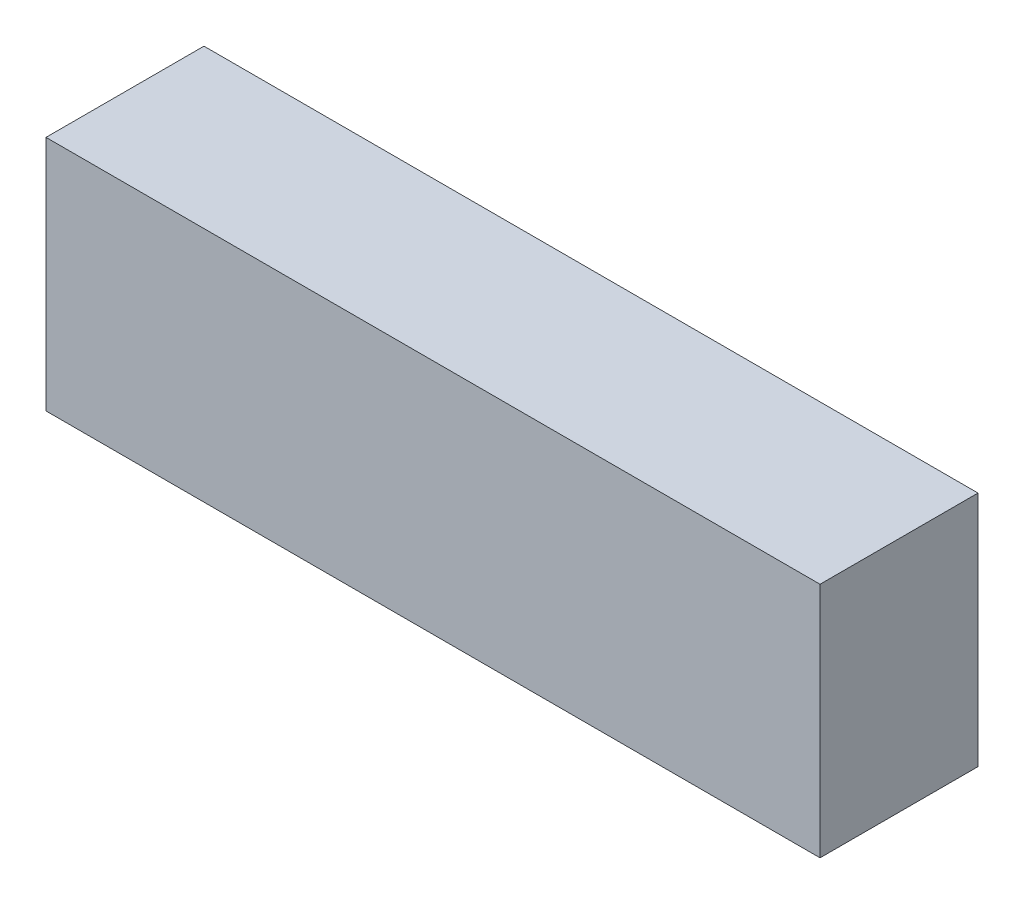
SolidWorks part; units mm, degrees
material "paste"
ref_plane "Ön Düzlem" through (0, 0, 0) normal (0, 0, 1) x (1, 0, 0)
ref_plane "Üst Düzlem" through (0, 0, 0) normal (0, 1, 0) x (1, 0, 0)
ref_plane "Sağ Düzlem" through (0, 0, 0) normal (1, 0, 0) x (0, 0, -1)
sketch "Sketch1" plane through (0, 0, 0) normal (0, 0, 1) x (1, 0, 0)
  line L1 (-23.0047, -9.4154) -> (25.9953, -9.4154)
  line L2 (-23.0047, -9.4154) -> (-23.0047, 5.5846)
  line L3 (-23.0047, 5.5846) -> (25.9953, 5.5846)
  line L4 (25.9953, -9.4154) -> (25.9953, 5.5846)
  dimension "D1" = 49
  dimension "D2" = 15
extrude "Boss-Extrude1" add sketch "Sketch1" along normal blind 10
